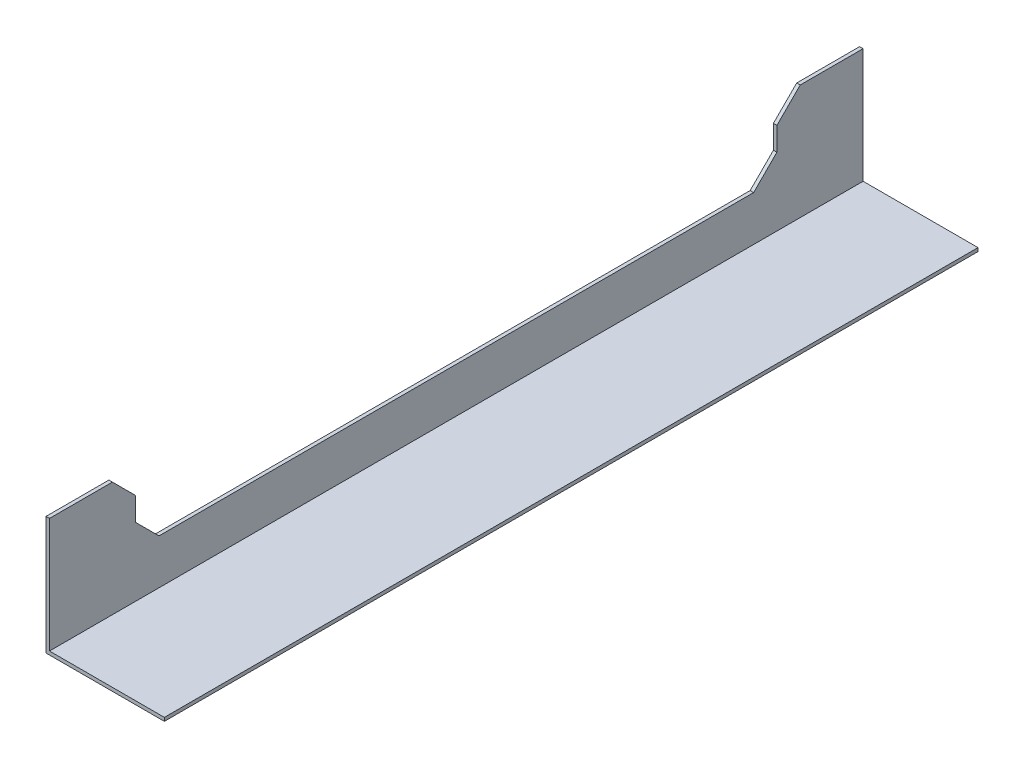
SolidWorks part; units mm, degrees
material "AISI 1015 Acero estirado en frío (SS)"
ref_plane "Alzado" through (0, 0, 0) normal (0, 0, 1) x (1, 0, 0)
ref_plane "Planta" through (0, 0, 0) normal (0, 1, 0) x (1, 0, 0)
ref_plane "Vista lateral" through (0, 0, 0) normal (1, 0, 0) x (0, 0, -1)
sketch "Croquis1" plane through (0, 0, 0) normal (0, 0, 1) x (1, 0, 0)
  line L0 (0, 0) -> (0, 50.8)
  line L1 (0, 0) -> (50.8, 0)
  line L2 (1.5, 1.5) -> (50.8, 1.5)
  line L3 (1.5, 1.5) -> (1.5, 50.8)
  line L4 (1.5, 50.8) -> (0, 50.8)
  line L5 (50.8, 1.5) -> (50.8, 0)
  dimension "D1" = 50.8
  dimension "D2" = 1.5
extrude "Saliente-Extruir1" add sketch "Croquis1" along normal blind 349.2
sketch "Croquis2" plane through (0, 0, 0) normal (-1, 0, 0) x (0, 0, 1)
  line L0 (349.2, 25.4) -> (-34.0342, 25.4) construction
  line L1 (349.2, 50.8) -> (349.2, 0) construction
  line L2 (174.6, 0) -> (174.6, 64.0617) construction
  line L3 (349.2, 0) -> (0, 0) construction
  circle A0 centre (126.6, 25.4) radius 4
  circle A1 centre (222.6, 25.4) radius 4
  circle A2 centre (30.6, 25.4) radius 4
  circle A3 centre (318.6, 25.4) radius 4
  dimension "D1" = 8
  dimension "D2" = 48
  dimension "D3" = 48
  dimension "D4" = 96
  dimension "D5" = 96
extrude "Cortar-Extruir1" [suppressed] cut sketch "Croquis2" against normal blind 2
sketch "Croquis5" plane through (0, 0, 0) normal (-1, 0, 0) x (0, 0, 1)
  line L0 (174.6, 0) -> (174.6, 50.8) construction
  line L1 (349.2, 0) -> (0, 0) construction
  line L2 (349.2, 50.8) -> (0, 50.8) construction
  line L3 (312.2, 0) -> (312.2, 50.8) construction
  line L4 (349.2, 50.8) -> (349.2, 0) construction
  line L5 (349.2, 20.8) -> (0, 20.8) construction
  line L6 (0, 50.8) -> (0, 0) construction
  line L7 (312.2, 50.8) -> (312.2, 20.8)
  line L8 (312.2, 20.8) -> (37, 20.8)
  line L9 (37, 50.8) -> (37, 20.8)
  point P16 (174.6, 20.8)
  dimension "D1" = 37
  dimension "D2" = 30
extrude "Cortar-Extruir2" cut sketch "Croquis5" against normal blind 2 and the other way through all
chamfer "Chaflán1" distance 10 angle 45 4 edges at (0.75, 50.8, 37) (0.75, 20.8, 37) (0.75, 20.8, 312.2) (0.75, 50.8, 312.2)
